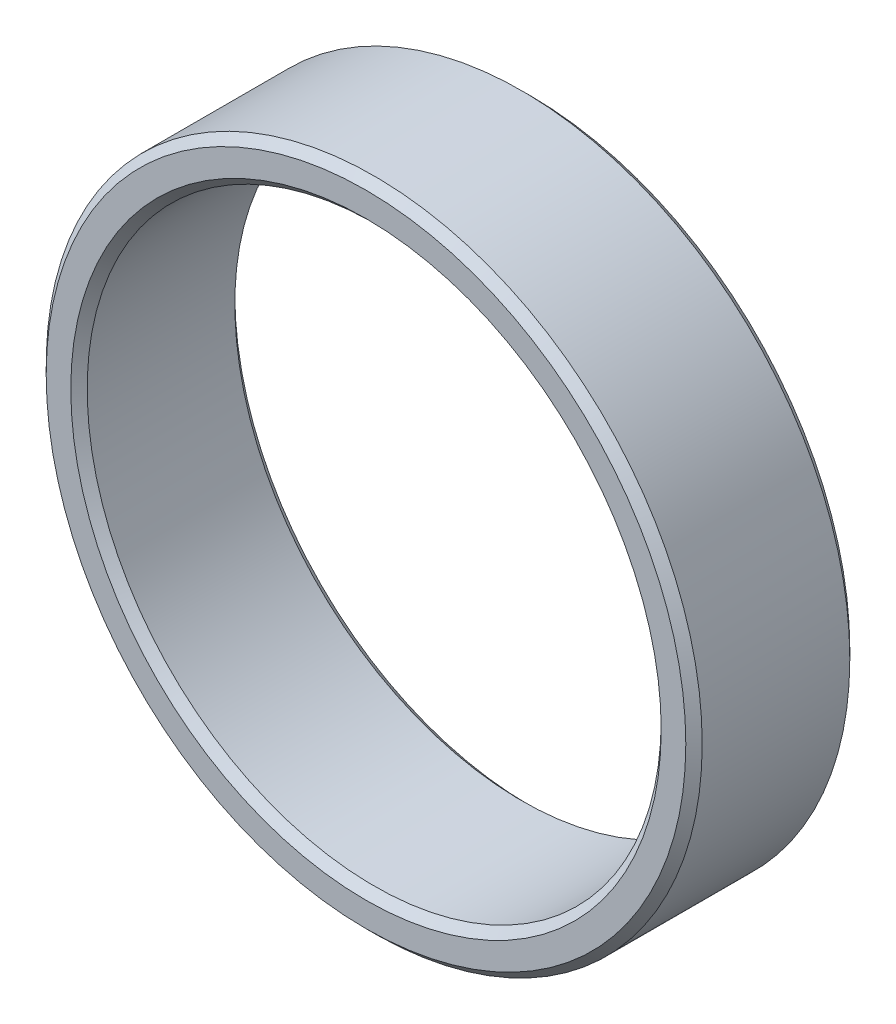
SolidWorks part; units mm, degrees
ref_plane "Plan1" through (0, 0, 0) normal (0, 0, 1) x (1, 0, 0)
ref_plane "Plan2" through (0, 0, 0) normal (0, 1, 0) x (1, 0, 0)
ref_plane "Plan3" through (0, 0, 0) normal (1, 0, 0) x (0, 0, -1)
sketch "Esquisse1" plane through (0, 0, 0) normal (0, 0, 1) x (1, 0, 0)
  circle A0 centre (0, 0) radius 7
  circle A1 centre (0, 0) radius 8
  dimension "D1" = 16
  dimension "D2" = 14
extrude "Base-Extrusion" add sketch "Esquisse1" along normal blind 4
chamfer "Chanfrein1" distance 0.2 angle 45
